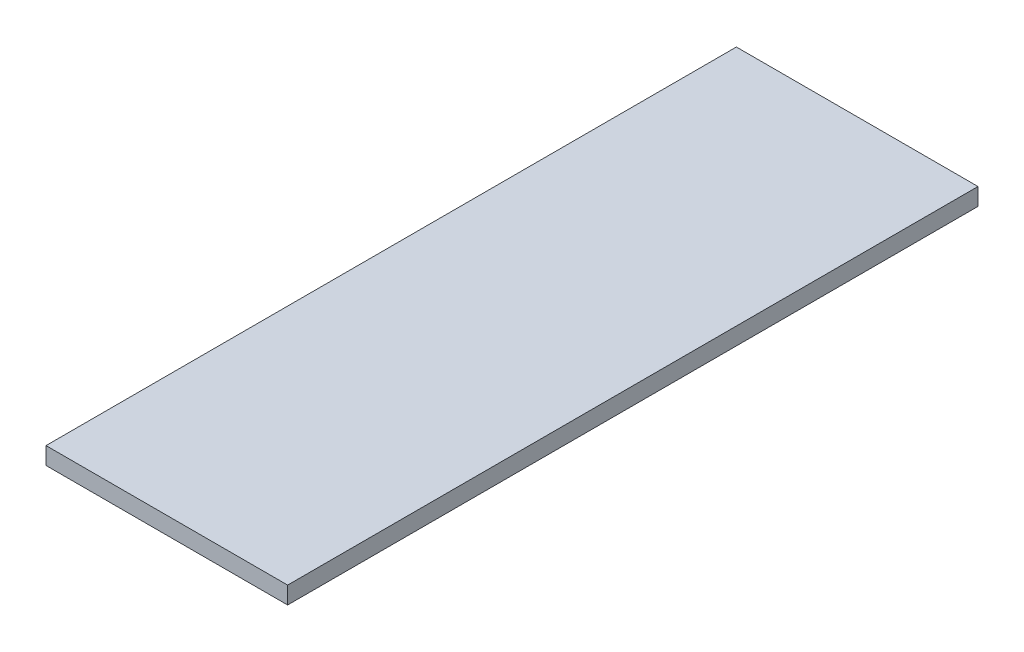
SolidWorks part; units mm, degrees
ref_plane "Front Plane" through (0, 0, 0) normal (0, 0, 1) x (1, 0, 0)
ref_plane "Top Plane" through (0, 0, 0) normal (0, 1, 0) x (1, 0, 0)
ref_plane "Right Plane" through (0, 0, 0) normal (1, 0, 0) x (0, 0, -1)
sketch "Sketch1" plane through (0, 0, 0) normal (0, 1, 0) x (1, 0, 0)
  line L1 (16.2385, 100.4587) -> (86.2385, 100.4587)
  line L2 (16.2385, 100.4587) -> (16.2385, -99.5413)
  line L3 (16.2385, -99.5413) -> (86.2385, -99.5413)
  line L4 (86.2385, 100.4587) -> (86.2385, -99.5413)
  line L5 (16.2385, 100.4587) -> (86.2385, -99.5413) construction
  line L6 (16.2385, -99.5413) -> (86.2385, 100.4587) construction
  point P4 (51.2385, 0.4587)
  dimension "D1" = 200
  dimension "D2" = 70
extrude "Boss-Extrude1" add sketch "Sketch1" along normal blind 5
